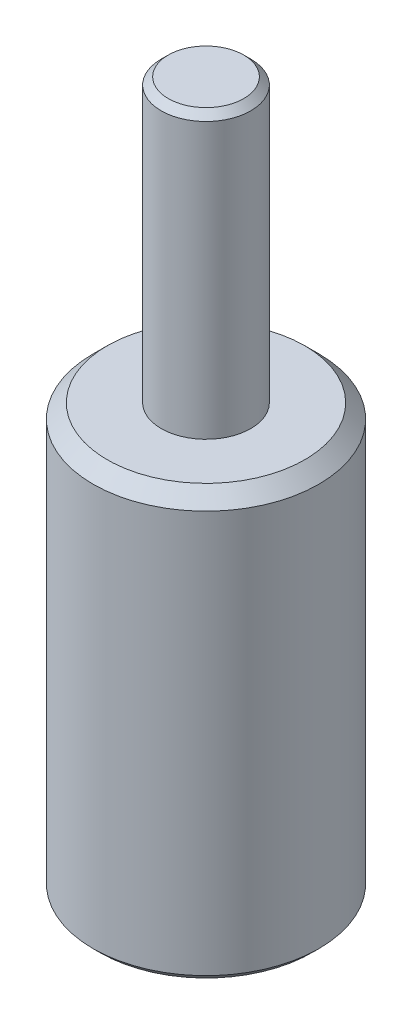
SolidWorks part; units mm, degrees
material "AISI 1010 Barre d'acier laminée à chaud"
ref_plane "Plan de face" through (0, 0, 0) normal (0, 0, 1) x (1, 0, 0)
ref_plane "Plan de dessus" through (0, 0, 0) normal (0, 1, 0) x (1, 0, 0)
ref_plane "Plan de droite" through (0, 0, 0) normal (1, 0, 0) x (0, 0, -1)
sketch "Esquisse1" plane through (0, 0, 0) normal (0, 0, 1) x (1, 0, 0)
  line L0 (0, 0) -> (8, 0)
  line L1 (8, 0) -> (8, 30)
  line L2 (8, 30) -> (3.175, 30)
  line L3 (3.175, 30) -> (3.175, 50)
  line L4 (3.175, 50) -> (0, 50)
  line L5 (0, 50) -> (0, 0)
  point P0 (0, 0)
  dimension "D1" = 3.175
  dimension "D2" = 8
  dimension "D3" = 30
  dimension "D4" = 20
revolve "Révolution1" add sketch "Esquisse1" angle 360 about L5
chamfer "Chanfrein1" distance 1 angle 45 1 edges at (0, 30, 8)
chamfer "Chanfrein2" distance 0.5 angle 45 2 edges at (0, 0, 8) (0, 50, 3.175)
hole_wizard "Diamètre du perçage Ø6.3 (6.3)1" positions "Esquisse2" profile "Esquisse3" hole size "Ø6.3" standard "ISO"
sketch "Esquisse2" plane through (0, 0, 0) normal (0, -1, 0) x (-1, 0, 0)
  point P0 (0, 0)
sketch "Esquisse3" plane through (0, 0, 0) normal (1, 0, 0) x (0, 0, -1)
  line L0 (0, 0) -> (0, 21.9077)
  line L1 (0, 21.9077) -> (3.175, 20)
  line L2 (3.175, 20) -> (3.175, 0)
  line L5 (3.175, 0) -> (0, 0)
  line L10 (0, 21.9077) -> (-3.175, 20) construction
  line L11 (0, -6.35) -> (0, 107.95) construction
  dimension "Diamètre du perçage" = 6.35
  dimension "Profondeur du perçage" = 20
  dimension "Angle de pointe" = 118
